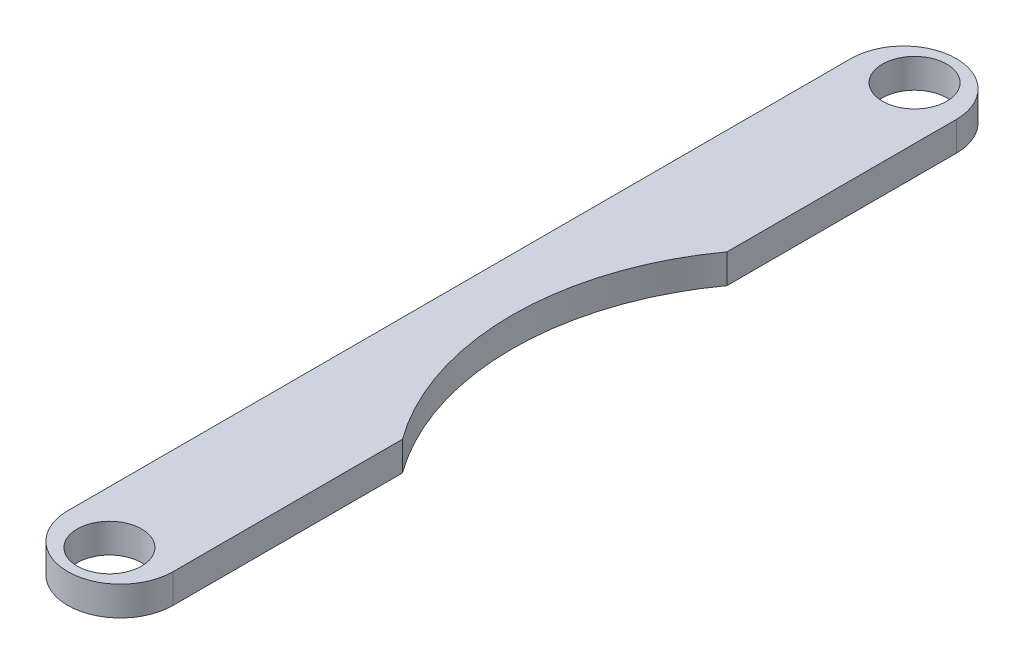
SolidWorks part; units mm, degrees
material "AISI 316 Stainless Steel Sheet (SS)"
ref_plane "Front Plane" through (0, 0, 0) normal (0, 0, 1) x (1, 0, 0)
ref_plane "Top Plane" through (0, 0, 0) normal (0, 1, 0) x (1, 0, 0)
ref_plane "Right Plane" through (0, 0, 0) normal (1, 0, 0) x (0, 0, -1)
sketch "Sketch1" plane through (0, 0, 0) normal (0, 1, 0) x (1, 0, 0)
  line L0 (0, -13.375) -> (0, 13.375) construction
  line L1 (-1.8, -13.375) -> (-1.8, 13.375)
  line L2 (1.8, -13.375) -> (1.8, 13.375)
  arc A0 (-1.8, -13.375) -> (1.8, -13.375) centre (0, -13.375) ccw
  arc A1 (1.8, 13.375) -> (-1.8, 13.375) centre (0, 13.375) ccw
  circle A2 centre (0, -13.75) radius 1.1
  circle A3 centre (0, 13.75) radius 1.1
  point P2 (0, 0)
  point P12 (0, 13.4277)
  point P13 (0, 0)
  dimension "D3" = 2.2
  dimension "D1" = 26.75
  dimension "D2" = 3.6
  dimension "D4" = 0.375
  dimension "D5" = 0.375
extrude "Boss-Extrude1" add sketch "Sketch1" along normal blind 1
ref_plane "Plane1" through (0, 0, 0) normal (0.7071, 0.7071, 0) x (0.7071, -0.7071, 0)
sketch "Sketch3" plane through (0, 0, 0) normal (0.7071, 0.7071, 0) x (0.7071, -0.7071, 0)
  circle A0 centre (12.7, 0) radius 12.7
  point P2 (0, 0)
  dimension "D2" = 25.4
  dimension "D1" = 12.7
extrude "Cut-Extrude1" cut sketch "Sketch3" against normal through all both and the other way through all
sketch "Sketch4" plane through (0, 0, 0) normal (0, -1, 0) x (1, 0, 0)
  circle A0 centre (9.4303, 0) radius 9.4303
extrude "Cut-Extrude2" cut sketch "Sketch4" against normal up to next
